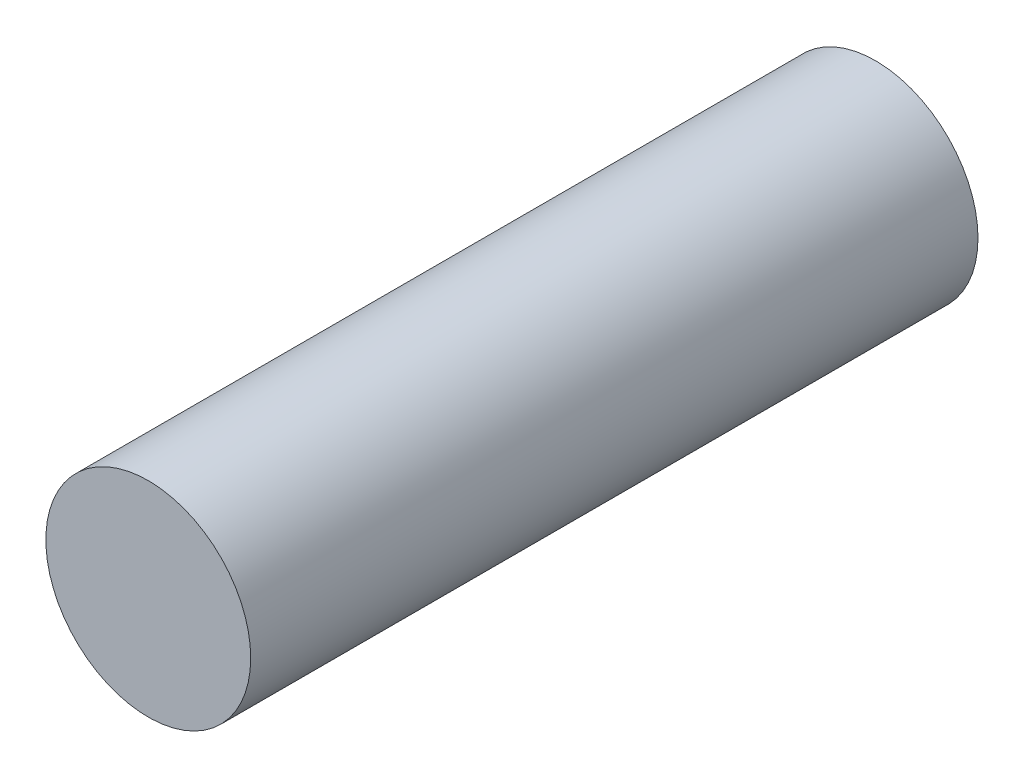
SolidWorks part; units mm, degrees
material "AISI 1045 钢，冷拔"
ref_plane "前视基准面" through (0, 0, 0) normal (0, 0, 1) x (1, 0, 0)
ref_plane "上视基准面" through (0, 0, 0) normal (0, 1, 0) x (1, 0, 0)
ref_plane "右视基准面" through (0, 0, 0) normal (1, 0, 0) x (0, 0, -1)
sketch "草图1" plane through (0, 0, 0) normal (0, 0, 1) x (1, 0, 0)
  circle A1 centre (0, 0) radius 20
  dimension "D1" = 40
extrude "凸台-拉伸1" add sketch "草图1" against normal blind 142
